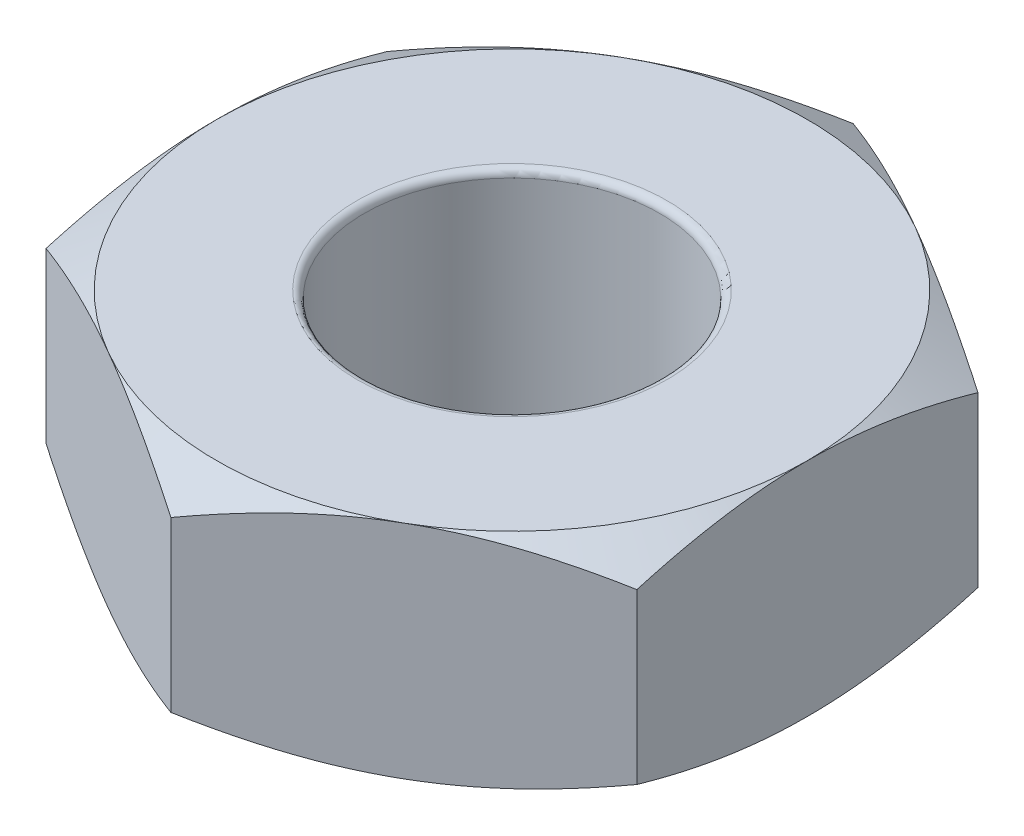
SolidWorks part; units mm, degrees
ref_plane "Front Plane" through (0, 0, 0) normal (0, 0, 1) x (1, 0, 0)
ref_plane "Top Plane" through (0, 0, 0) normal (0, 1, 0) x (1, 0, 0)
ref_plane "Right Plane" through (0, 0, 0) normal (1, 0, 0) x (0, 0, -1)
sketch "Sketch2" plane through (0, 0, 0) normal (0, 1, 0) x (1, 0, 0)
  line L1 (2, -1.1547) -> (2, 1.1547)
  line L2 (2, 1.1547) -> (0, 2.3094)
  line L3 (0, 2.3094) -> (-2, 1.1547)
  line L4 (-2, 1.1547) -> (-2, -1.1547)
  line L5 (-2, -1.1547) -> (0, -2.3094)
  line L6 (0, -2.3094) -> (2, -1.1547)
  circle A0 centre (0, 0) radius 1
  circle A1 centre (0, 0) radius 2 construction
  dimension "D1" = 2
  dimension "D2" = 4
extrude "Boss-Extrude1" add sketch "Sketch2" along normal blind 1.5
sketch "Sketch3" plane through (0, 1.5, 0) normal (0, 1, 0) x (1, 0, 0)
  circle A0 centre (0, 0) radius 2 construction
  circle A1 centre (0, 0) radius 2
extrude "Cut-Extrude1" cut sketch "Sketch3" against normal blind 2 draft 60 flip side to cut
sketch "Sketch4" plane through (0, 0, 0) normal (0, -1, 0) x (1, 0, 0)
  circle A0 centre (0, 0) radius 2 construction
  circle A1 centre (0, 0) radius 2
extrude "Cut-Extrude2" cut sketch "Sketch4" against normal blind 2 draft 60 flip side to cut
fillet "Fillet1" radius 0.05 2 edges at (0, 0, 1) (0, 1.5, 1)
